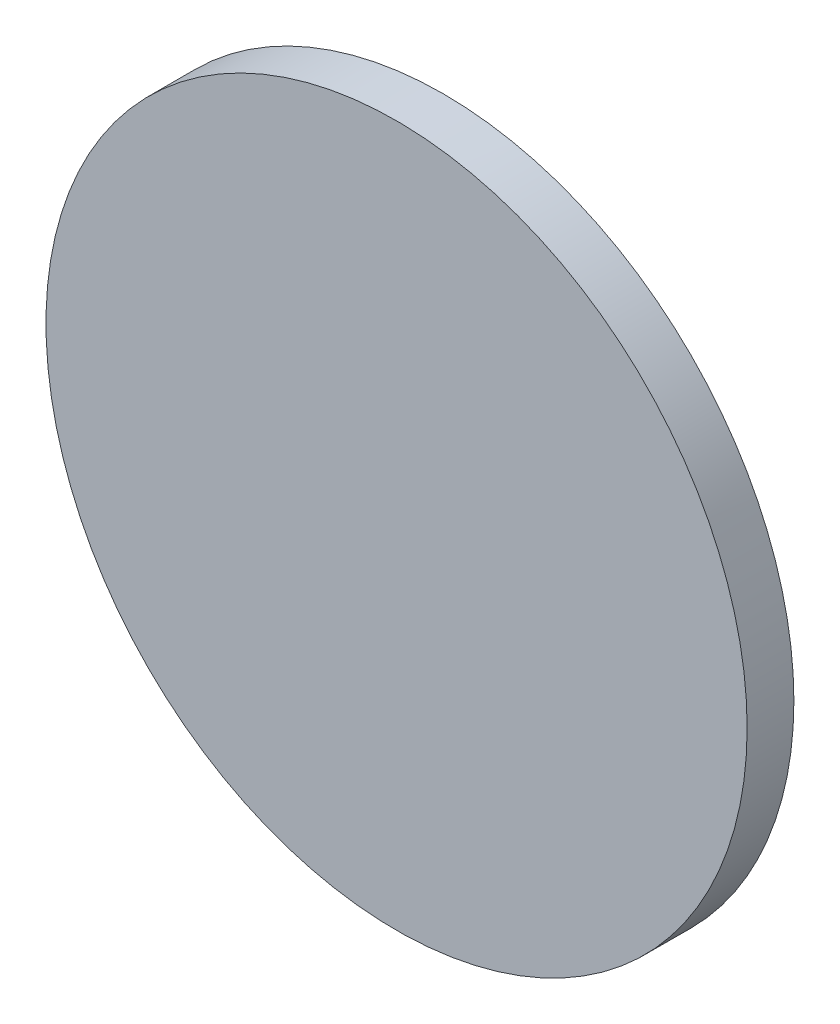
SolidWorks part; units mm, degrees
ref_plane "前视基准面" through (0, 0, 0) normal (0, 0, 1) x (1, 0, 0)
ref_plane "上视基准面" through (0, 0, 0) normal (0, 1, 0) x (1, 0, 0)
ref_plane "右视基准面" through (0, 0, 0) normal (1, 0, 0) x (0, 0, -1)
sketch "草图1" plane through (0, 0, 0) normal (0, 0, 1) x (1, 0, 0)
  line L1 (30, 30) -> (-30, 30)
  line L2 (30, 30) -> (30, -30)
  line L3 (30, -30) -> (-30, -30)
  line L4 (-30, 30) -> (-30, -30)
  line L5 (30, 30) -> (-30, -30) construction
  line L6 (30, -30) -> (-30, 30) construction
  point P0 (0, 0)
ref_plane "基准面4" through (0, 0, 50) normal (0, 0, 1) x (1, 0, 0)
sketch "草图2" plane through (0, 0, 50) normal (0, 0, 1) x (1, 0, 0)
  circle A0 centre (0, 0) radius 150
  dimension "D1" = 300
loft "放样1" add profiles "草图2", "草图1"
sketch "草图3" plane through (0, 0, 50) normal (0, 0, 1) x (1, 0, 0)
  arc A4 (-106.066, -106.066) -> (106.066, -106.066) centre (0, 0) ccw
  arc A5 (106.066, -106.066) -> (106.066, 106.066) centre (0, 0) ccw
  arc A6 (106.066, 106.066) -> (-106.066, 106.066) centre (0, 0) ccw
  arc A7 (-106.066, 106.066) -> (-106.066, -106.066) centre (0, 0) ccw
  arc A8 (-106.066, -106.066) -> (106.066, -106.066) centre (0, 0) ccw
  arc A9 (106.066, -106.066) -> (106.066, 106.066) centre (0, 0) ccw
  arc A10 (106.066, 106.066) -> (-106.066, 106.066) centre (0, 0) ccw
  arc A11 (-106.066, 106.066) -> (-106.066, -106.066) centre (0, 0) ccw
  dimension "D1" = 0
extrude "凸台-拉伸1" add sketch "草图3" along normal blind 20
